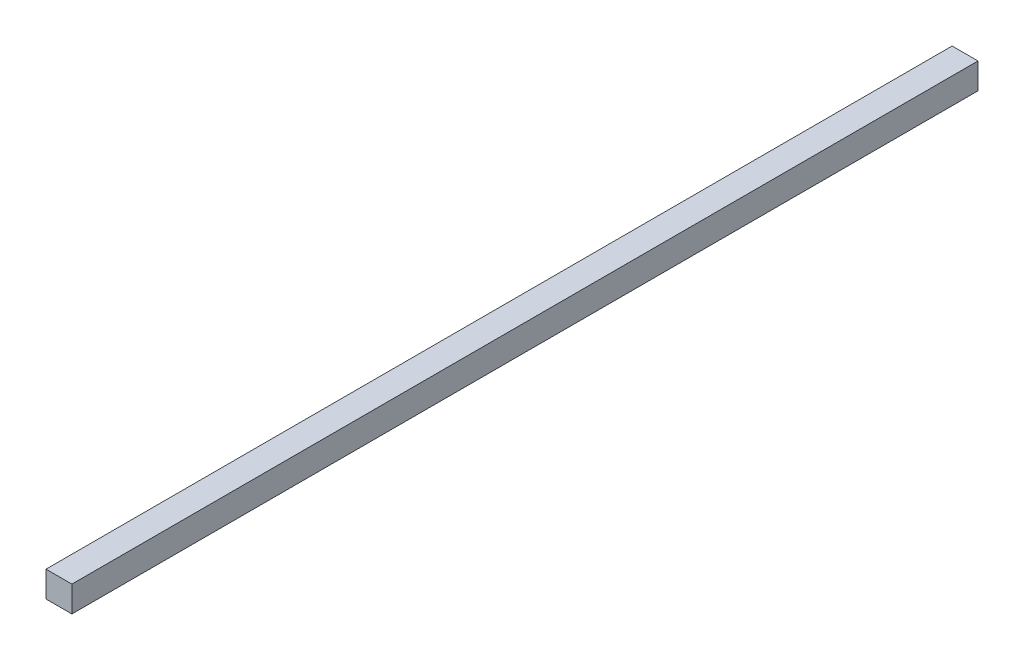
SolidWorks part; units mm, degrees
ref_plane "Plan de face" through (0, 0, 0) normal (0, 0, 1) x (1, 0, 0)
ref_plane "Plan de dessus" through (0, 0, 0) normal (0, 1, 0) x (1, 0, 0)
ref_plane "Plan de droite" through (0, 0, 0) normal (1, 0, 0) x (0, 0, -1)
sketch "Esquisse1" plane through (0, 0, 0) normal (0, 0, 1) x (1, 0, 0)
  line L1 (-5, 5) -> (5, 5)
  line L2 (-5, 5) -> (-5, -5)
  line L3 (-5, -5) -> (5, -5)
  line L4 (5, 5) -> (5, -5)
  point P4 (0, -5)
  point P6 (-5, 0)
  dimension "D1" = 10
extrude "Boss.-Extru.1" add sketch "Esquisse1" along normal blind 350
